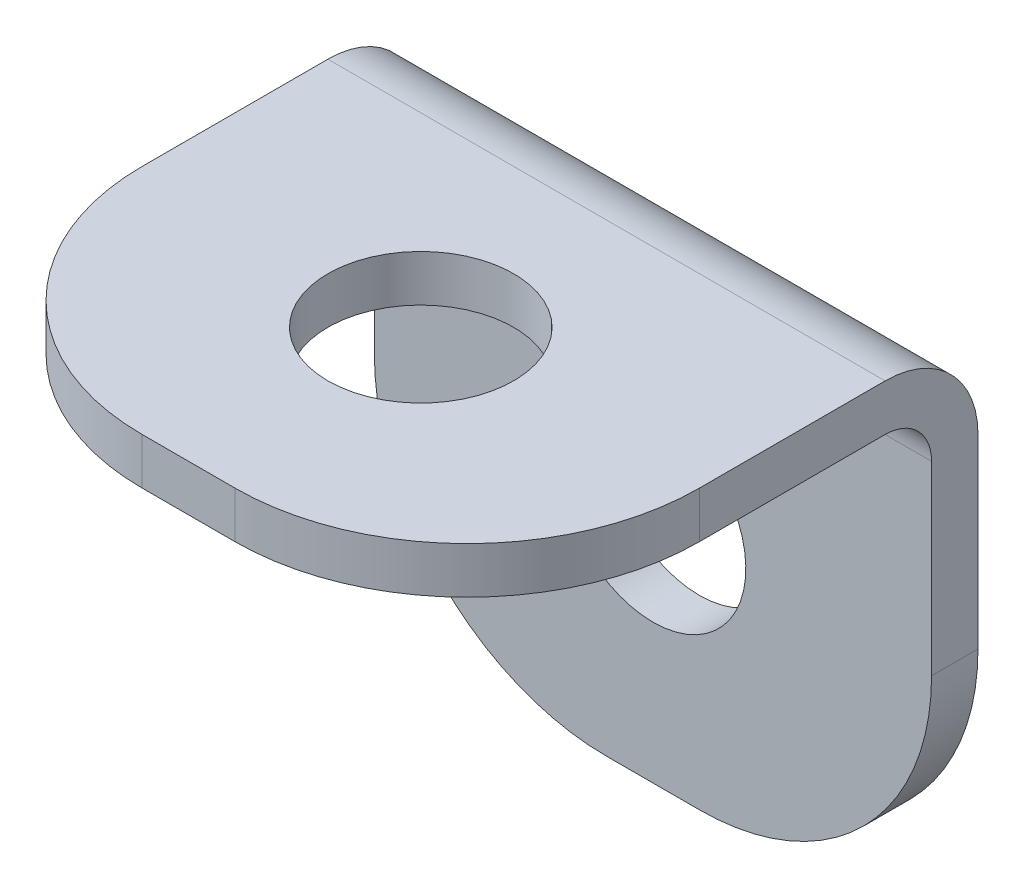
SolidWorks part; units mm, degrees
ref_plane "Front Plane" through (0, 0, 0) normal (0, 0, 1) x (1, 0, 0)
ref_plane "Top Plane" through (0, 0, 0) normal (0, 1, 0) x (1, 0, 0)
ref_plane "Right Plane" through (0, 0, 0) normal (1, 0, 0) x (0, 0, -1)
sketch "Sketch1" plane through (0, 0, 0) normal (0, 1, 0) x (1, 0, 0)
  line L0 (-6, 0) -> (-6, 1)
  line L1 (-1, -10) -> (1, -10)
  line L2 (-6, -5) -> (-6, 0)
  line L3 (-6, 0) -> (6, 0) construction
  line L4 (6, -5) -> (6, 0)
  line L5 (-6, 1) -> (6, 1)
  line L6 (6, 1) -> (6, 0)
  arc A0 (-1, -10) -> (-6, -5) centre (-1, -5) cw
  arc A1 (1, -10) -> (6, -5) centre (1, -5) ccw
  circle A2 centre (0, -5) radius 2
  point P4 (0, 0)
  point P10 (6, -10)
  dimension "D3" = 5
  dimension "D4" = 4
  dimension "D1" = 12
  dimension "D2" = 10
  dimension "D5" = 1
extrude "Extrude1" add sketch "Sketch1" along normal blind 1
ref_plane "Plane1" through (0, 0, 0) normal (0, -0.7071, -0.7071) x (-1, 0, 0)
mirror "Mirror2" about plane through (0, 0, 0) normal (0, -0.7071, -0.7071) of "Extrude1"
fillet "Fillet2" radius 1 1 edges at (0, 0, 0)
fillet "Fillet3" radius 2 1 edges at (0, 1, -1)
